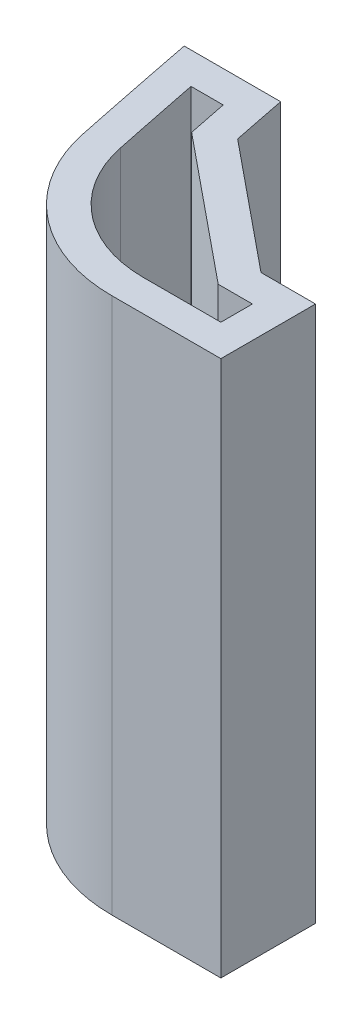
SolidWorks part; units mm, degrees
ref_plane "Front Plane" through (0, 0, 0) normal (0, 0, 1) x (1, 0, 0)
ref_plane "Top Plane" through (0, 0, 0) normal (0, 1, 0) x (1, 0, 0)
ref_plane "Right Plane" through (0, 0, 0) normal (1, 0, 0) x (0, 0, -1)
sketch "Sketch1" plane through (0, 0, 0) normal (0, 1, 0) x (1, 0, 0)
  line L11 (1.3226, -4.0286) -> (4.7797, -4.0286)
  line L12 (4.7797, -4.0286) -> (4.7797, -1.0286)
  line L13 (4.7797, -1.0286) -> (3.0511, -1.0286)
  line L14 (-1.3254, 3.9714) -> (-4.3826, 3.9714)
  line L18 (-0.9849, 2.2671) -> (3.0511, -1.0286) construction
  line L19 (-0.9849, 2.2671) -> (3.0511, -1.0286)
  line L20 (3.7797, -3.0286) -> (3.7797, -2.0286)
  line L21 (3.7797, -2.0286) -> (2.6947, -2.0286)
  line L22 (-1.8938, 1.7183) -> (2.6947, -2.0286)
  line L23 (-2.1465, 2.9714) -> (-3.1662, 2.9714)
  line L24 (1.3226, -3.0286) -> (3.7797, -3.0286)
  arc A6 (-4.3826, 3.9714) -> (-3.5728, -0.046) centre (330.9203, 69.4714) ccw
  arc A7 (-3.5728, -0.046) -> (1.3226, -4.0286) centre (1.3226, 0.9714) ccw
  arc A11 (-1.3254, 3.9714) -> (-0.9849, 2.2671) centre (330.9203, 69.4714) ccw
  arc A12 (-2.1465, 2.9714) -> (-1.8938, 1.7183) centre (330.9203, 69.4714) ccw
  arc A13 (-3.1662, 2.9714) -> (-2.5937, 0.1575) centre (330.9203, 69.4714) ccw
  arc A14 (-2.5937, 0.1575) -> (1.3226, -3.0286) centre (1.3226, 0.9714) ccw
  point P0 (-4.7862, 4.41)
  point P1 (-3.9763, 0.3926)
  point P2 (330.5168, 69.91)
  point P3 (0.9191, -3.59)
  point P5 (4.3762, -3.59)
  point P8 (-5.3927, 4.91)
  point P9 (330.5168, 69.91)
  point P10 (-4.4659, 0.2908)
  point P13 (0.9191, -4.09)
  point P14 (4.8762, -4.09)
  dimension "D1" = 1
extrude "Boss-Extrude1" add sketch "Sketch1" along normal blind 17
sketch "Sketch4" plane through (0.7167, 0, -0.8777) normal (0.6325, 0, -0.7746) x (-0.7746, 0, -0.6325)
  line L0 (-0.4086, 17) -> (-0.4086, 0) construction
  line L1 (-3.0139, 17) -> (2.1967, 17) construction
  line L2 (-3.0139, 0) -> (2.1967, 0) construction
  circle A0 centre (-0.4086, 8.5) radius 1.6
  dimension "D1" = 3.2
extrude "Cut-Extrude2" cut sketch "Sketch4" against normal up to surface (1 mm away) up to face at (0.4004, 8.5, 0.1552)
